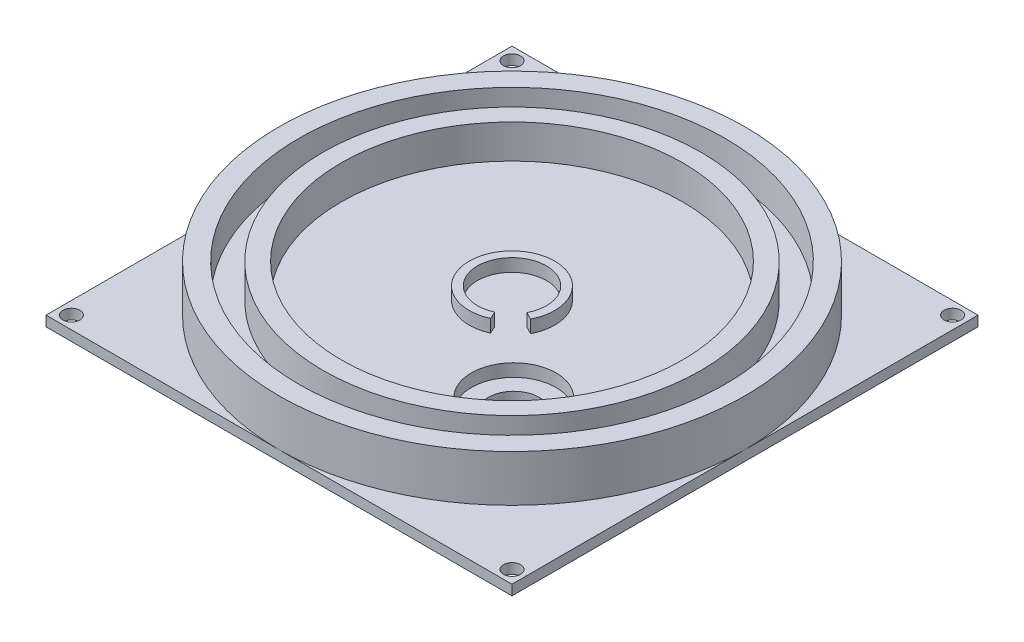
SolidWorks part; units mm, degrees
ref_plane "Front Plane" through (0, 0, 0) normal (0, 0, 1) x (1, 0, 0)
ref_plane "Top Plane" through (0, 0, 0) normal (0, 1, 0) x (1, 0, 0)
ref_plane "Right Plane" through (0, 0, 0) normal (1, 0, 0) x (0, 0, -1)
sketch "Sketch1" plane through (0, 0, 0) normal (0, 1, 0) x (1, 0, 0)
  circle A0 centre (0, 0) radius 69.85
  dimension "D1" = 139.7
extrude "Boss-Extrude1" add sketch "Sketch1" along normal blind 3.81
sketch "Sketch2" plane through (0, 3.81, 0) normal (0, 1, 0) x (1, 0, 0)
  circle A0 centre (0, 0) radius 69.85
  circle A1 centre (0, 0) radius 63.881
  circle A2 centre (0, 0) radius 56.6547
  circle A3 centre (0, 0) radius 51.181
  circle M2 centre (0, 0) radius 69.85
  dimension "D1" = 127.762
  dimension "D2" = 102.362
  dimension "D3" = 113.3094
extrude "Boss-Extrude2" add sketch "Sketch2" along normal blind 10.16 contours A1 M2 | A2 A3
sketch "Sketch3" plane through (0, 3.81, 0) normal (0, 1, 0) x (1, 0, 0)
  circle A0 centre (0, 0) radius 12.827
  circle A1 centre (0, 0) radius 10.3378
  dimension "D1" = 20.6756
  dimension "D2" = 25.654
extrude "Boss-Extrude3" add sketch "Sketch3" along normal blind 3.81
sketch "Sketch4" plane through (0, 7.62, 0) normal (0, 1, 0) x (1, 0, 0)
  line L0 (4.2386, -9.4289) -> (5.2592, -11.6993)
  line L2 (9.2002, -4.7145) -> (11.4155, -5.8496)
  circle A0 centre (0, 0) radius 12.827 construction
  arc A1 (4.2386, -9.4289) -> (9.2002, -4.7145) centre (0, 0) ccw
  circle A2 centre (0, 0) radius 10.3378 construction
  arc A3 (5.2592, -11.6993) -> (11.4155, -5.8496) centre (0, 0) ccw
  dimension "D1" = 10.3378
  dimension "D2" = 12.827
  dimension "D3" = 2.4892
  dimension "D4" = 2.4892
  dimension "D5" = 9.4289
  dimension "D6" = 9.2002
extrude "Cut-Extrude1" cut sketch "Sketch4" against normal blind 3.81
sketch "Sketch5" plane through (0, 3.81, 0) normal (0, 1, 0) x (1, 0, 0)
  circle A5 centre (25.4, -24.8868) radius 12.7
  dimension "D1" = 25.4
  dimension "D3" = 25.4
  dimension "D2" = 35.56
extrude "Cut-Extrude2" cut sketch "Sketch5" against normal blind 10.16
sketch "Sketch6" plane through (0, 0, 0) normal (0, -1, 0) x (1, 0, 0)
  line L1 (-69.85, 69.85) -> (69.85, 69.85)
  line L2 (-69.85, 69.85) -> (-69.85, -69.85)
  line L3 (-69.85, -69.85) -> (69.85, -69.85)
  line L4 (69.85, 69.85) -> (69.85, -69.85)
  line L5 (-69.85, 69.85) -> (69.85, -69.85) construction
  line L6 (-69.85, -69.85) -> (69.85, 69.85) construction
  point P0 (0, 0)
  dimension "D1" = 139.7
  dimension "D2" = 139.7
extrude "Boss-Extrude4" add sketch "Sketch6" along normal blind 3.048
sketch "Sketch7" plane through (0, 0, 0) normal (0, 1, 0) x (1, 0, 0)
  line L0 (-69.85, 0) -> (-69.85, 69.85) construction
  line L1 (-69.85, 69.85) -> (0, 69.85) construction
  line L2 (0, -69.85) -> (-69.85, -69.85) construction
  line L3 (-69.85, -69.85) -> (-69.85, 0) construction
  line L4 (69.85, -69.85) -> (0, -69.85) construction
  line L5 (69.85, 0) -> (69.85, -69.85) construction
  line L6 (69.85, 69.85) -> (69.85, 0) construction
  line L7 (0, 69.85) -> (69.85, 69.85) construction
  circle A0 centre (25.4, -24.8868) radius 7.62
  circle A1 centre (-66.04, -66.04) radius 2.54
  circle A2 centre (66.04, -66.04) radius 2.54
  circle A3 centre (66.04, 66.04) radius 2.54
  circle A4 centre (-66.04, 66.04) radius 2.54
  dimension "D1" = 15.24
  dimension "D2" = 5.08
  dimension "D3" = 5.08
  dimension "D4" = 5.08
  dimension "D5" = 5.08
  dimension "D11" = 3.81
  dimension "D6" = 3.81
  dimension "D7" = 3.81
  dimension "D8" = 3.81
  dimension "D9" = 3.81
  dimension "D10" = 3.81
  dimension "D12" = 3.81
  dimension "D13" = 3.81
extrude "Cut-Extrude3" cut sketch "Sketch7" against normal blind 3.048
